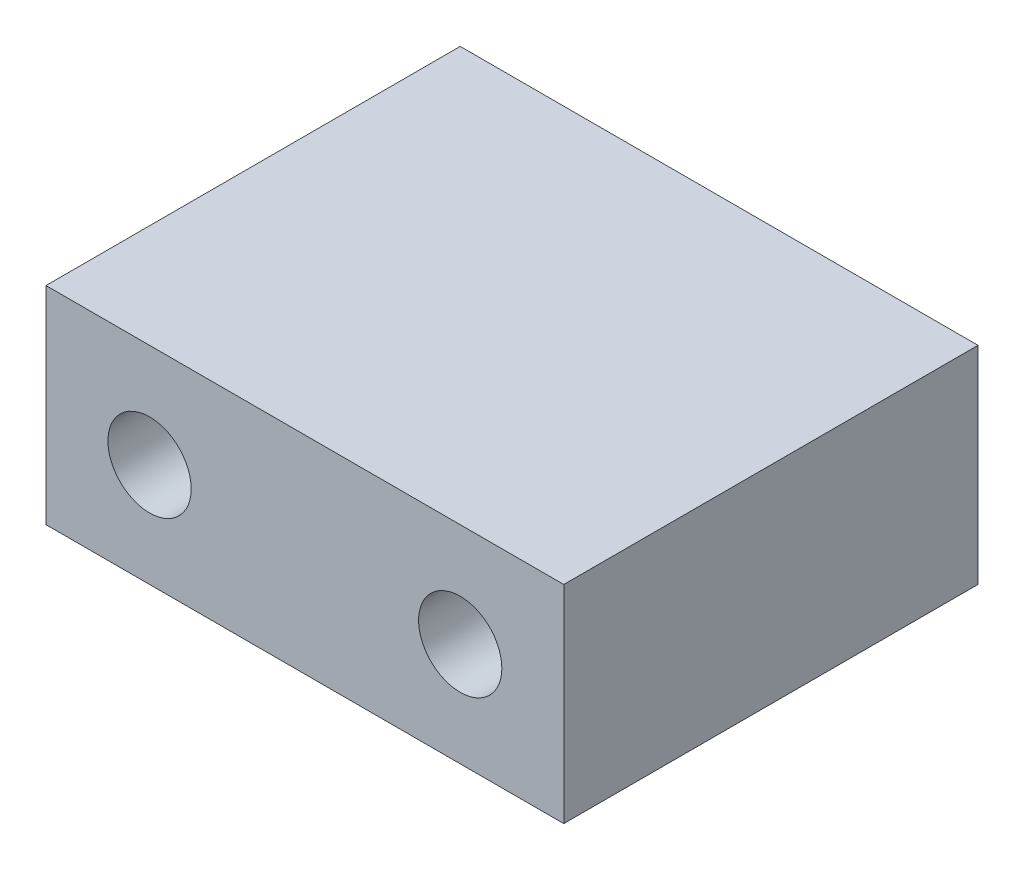
SolidWorks part; units mm, degrees
ref_plane "Front Plane" through (0, 0, 0) normal (0, 0, 1) x (1, 0, 0)
ref_plane "Top Plane" through (0, 0, 0) normal (0, 1, 0) x (1, 0, 0)
ref_plane "Right Plane" through (0, 0, 0) normal (1, 0, 0) x (0, 0, -1)
sketch "Sketch1" plane through (0, 0, 0) normal (0, 0, 1) x (1, 0, 0)
  line L1 (15.875, -6.35) -> (-15.875, -6.35)
  line L2 (15.875, -6.35) -> (15.875, 6.35)
  line L3 (15.875, 6.35) -> (-15.875, 6.35)
  line L4 (-15.875, -6.35) -> (-15.875, 6.35)
  line L5 (15.875, -6.35) -> (-15.875, 6.35) construction
  line L6 (15.875, 6.35) -> (-15.875, -6.35) construction
  point P0 (0, 0)
  dimension "D1" = 12.7
  dimension "D2" = 31.75
extrude "Boss-Extrude1" add sketch "Sketch1" along normal blind 25.4
hole_wizard "1/4-20 Tapped Hole1" positions "Sketch2" profile "Sketch3" tap size "1/4-20" standard "ANSI Inch"
sketch "Sketch2" plane through (0, 0, 25.4) normal (0, 0, 1) x (1, 0, 0)
  line L0 (-15.875, 6.35) -> (-15.875, -6.35) construction
  line L1 (15.875, -6.35) -> (15.875, 6.35) construction
  point P0 (-9.525, 0)
  point P2 (9.525, 0)
  dimension "D1" = 6.35
  dimension "D2" = 6.35
sketch "Sketch3" plane through (-9.525, 0, 25.4) normal (1, 0, 0) x (0, -1, 0)
  line L0 (0, 0) -> (0, 18.0438)
  line L1 (0, 18.0438) -> (2.5527, 16.51)
  line L2 (2.5527, 16.51) -> (2.5527, 0)
  line L5 (2.5527, 0) -> (0, 0)
  line L10 (0, 18.0438) -> (-2.5527, 16.51) construction
  line L11 (0, -6.35) -> (0, 107.95) construction
  dimension "Tap Drill Dia." = 5.1054
  dimension "Tap Drill Depth" = 16.51
  dimension "Drill Angle" = 118
cosmetic thread "Hole Thread1" parameters "D1"=12.7, "D2"=6.35
cosmetic thread "Hole Thread2" parameters "D1"=12.7, "D2"=6.35
